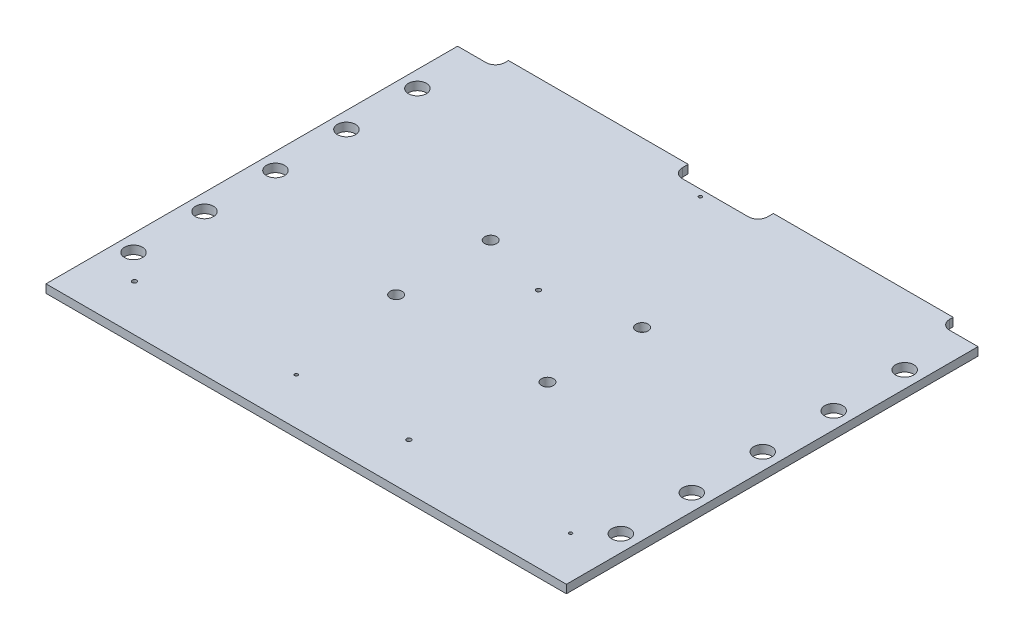
SolidWorks part; units mm, degrees
ref_plane "Front Plane" through (0, 0, 0) normal (0, 0, 1) x (1, 0, 0)
ref_plane "Top Plane" through (0, 0, 0) normal (0, 1, 0) x (1, 0, 0)
ref_plane "Right Plane" through (0, 0, 0) normal (1, 0, 0) x (0, 0, -1)
sketch "Sketch1" plane through (0, 0, 0) normal (0, 1, 0) x (1, 0, 0)
  line L0 (0, 0) -> (110, 0)
  line L1 (110, 0) -> (110, 87)
  line L2 (0, 0) -> (110, 0) construction
  line L3 (0, 0) -> (0, 87)
  line L4 (0, 87) -> (110, 87) construction
  line L5 (0, 89.75) -> (110, 89.75) construction
  line L6 (102, 89.75) -> (102, 89)
  line L7 (0, 0) -> (110, 0) construction
  line L8 (110, 89.75) -> (110, 0) construction
  line L9 (104, 87) -> (110, 87)
  line L10 (102, 89.75) -> (64, 89.75)
  line L11 (48, 86.5) -> (62, 86.5)
  line L12 (110, 0) -> (110, 89.75) construction
  line L13 (110, 89.75) -> (0, 89.75) construction
  line L14 (0, 89.75) -> (0, 0) construction
  line L15 (8, 89.75) -> (46, 89.75)
  line L16 (64, 89.75) -> (64, 88.5)
  line L18 (0, 87) -> (6, 87)
  line L20 (8, 89.75) -> (8, 89)
  line L21 (46, 89.75) -> (46, 88.5)
  arc A2 (46, 88.5) -> (48, 86.5) centre (48, 88.5) ccw
  arc A3 (102, 89) -> (104, 87) centre (104, 89) ccw
  arc A4 (64, 88.5) -> (62, 86.5) centre (62, 88.5) cw
  arc A8 (8, 89) -> (6, 87) centre (6, 89) cw
extrude "FR4" add sketch "Sketch1" along normal blind 1.7526
ref_plane "center-of-slot" through (0, 0.8763, 0) normal (0, -1, 0) x (-1, 0, 0)
sketch "Sketch7" plane through (0, 1.7526, 0) normal (0, 1, 0) x (1, 0, 0)
  circle A0 centre (3.5, 15) radius 1.905
  circle A1 centre (106.5, 15) radius 1.905
  circle A2 centre (106.5, 30) radius 1.905
  circle A3 centre (106.5, 45) radius 1.905
  circle A4 centre (106.5, 60) radius 1.905
  circle A5 centre (106.5, 75) radius 1.905
  circle A6 centre (3.5, 30) radius 1.905
  circle A7 centre (3.5, 45) radius 1.905
  circle A8 centre (3.5, 60) radius 1.905
  circle A9 centre (3.5, 75) radius 1.905
  dimension "D1" = 2
  dimension "D2" = 5
extrude "thermal-wall-holes-sides" cut sketch "Sketch7" against normal through all
sketch "Sketch8" plane through (0, 1.7526, 0) normal (0, 1, 0) x (1, 0, 0)
  line L0 (53.2, 86.5) -> (53.2, 0) construction
  line L1 (62, 86.5) -> (48, 86.5) construction
  line L2 (0, 0) -> (110, 0) construction
  circle A0 centre (8.9, 9.8) radius 0.47
  circle A1 centre (66.9, 9.8) radius 0.47
  circle A2 centre (53.2, 50.9) radius 0.47
  circle A3 centre (53.2, 85.1) radius 0.33
  circle A4 centre (43.1, 9.8) radius 0.33
  circle A5 centre (101.1, 9.8) radius 0.33
  dimension "D1" = 2
  dimension "D2" = 1
extrude "controlled-depth-holes.top" cut sketch "Sketch8" against normal blind 1.1176
sketch "Sketch9" plane through (0, 0, 0) normal (0, -1, 0) x (1, 0, 0)
  line L0 (53.5, -86.5) -> (53.5, 0) construction
  line L1 (62, -86.5) -> (48, -86.5) construction
  line L2 (0, 0) -> (110, 0) construction
  circle A0 centre (8.975, -9.5) radius 0.47
  circle A1 centre (66.975, -9.5) radius 0.47
  circle A2 centre (53.5, -50.975) radius 0.47
  circle A3 centre (53.5, -85.175) radius 0.32
  circle A4 centre (43.175, -9.5) radius 0.33
  circle A5 centre (101.175, -9.5) radius 0.33
  dimension "D1" = 2
  dimension "D2" = 1
extrude "controlled-depth-holes.bottom" cut sketch "Sketch9" against normal blind 1.1176
sketch "Sketch10" plane through (0, 1.7526, 0) normal (0, 1, 0) x (1, 0, 0)
  line L0 (0, 35) -> (110, 35) construction
  line L1 (0, 87) -> (0, 0) construction
  line L2 (110, 0) -> (110, 87) construction
  line L3 (110, 55) -> (0, 55) construction
  line L4 (39, 55) -> (39, 35) construction
  line L6 (71, 55) -> (71, 35) construction
  circle A0 centre (39, 55) radius 1.27
  circle A1 centre (71, 55) radius 1.27
  circle A2 centre (71, 35) radius 1.27
  circle A3 centre (39, 35) radius 1.27
extrude "thermal-screw-holes-middle" cut sketch "Sketch10" against normal through all
